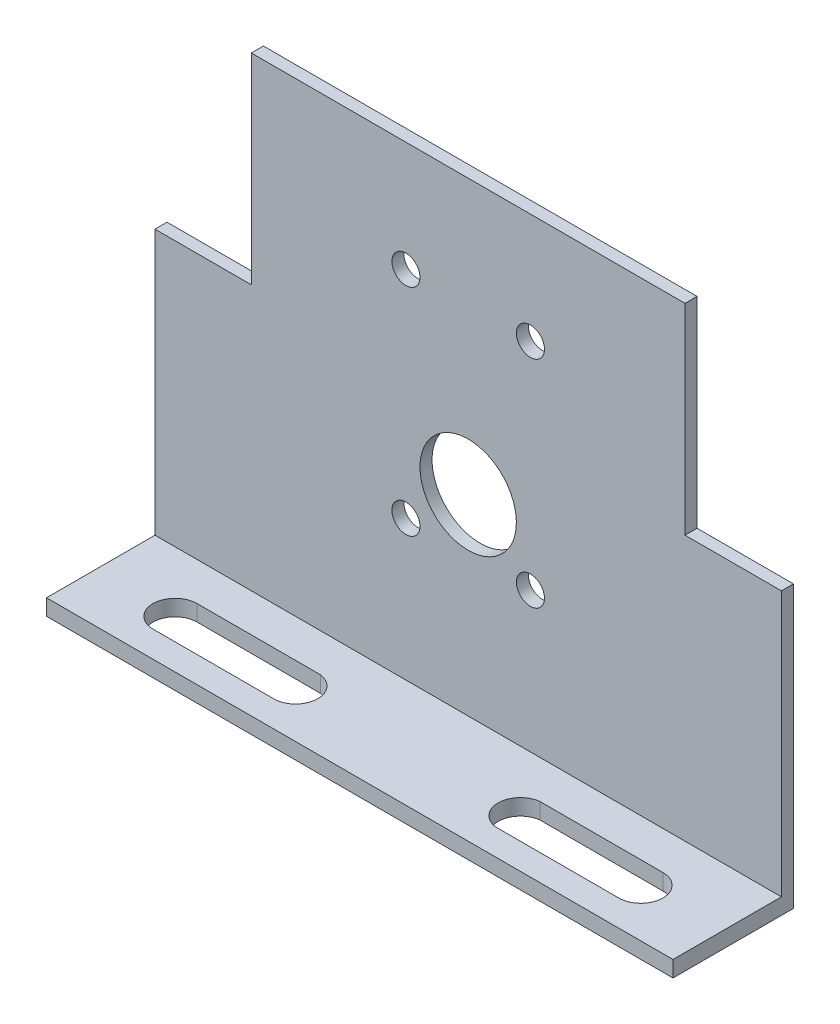
SolidWorks part; units mm, degrees
ref_plane "前视基准面" through (0, 0, 0) normal (0, 0, 1) x (1, 0, 0)
ref_plane "上视基准面" through (0, 0, 0) normal (0, 1, 0) x (1, 0, 0)
ref_plane "右视基准面" through (0, 0, 0) normal (1, 0, 0) x (0, 0, -1)
sketch "草图1" plane through (0, 0, 0) normal (0, 0, 1) x (1, 0, 0)
  line L0 (-78, 0) -> (0, 0)
  line L2 (0, 0) -> (0, 2)
  line L3 (-78, 0) -> (-78, 2)
  line L5 (-78, 2.7366) -> (-78, 2)
  line L6 (0, 2) -> (0, 2.7366)
  line L7 (-78, 2.7366) -> (-78, 35)
  line L8 (-78, 35) -> (-66, 35)
  line L9 (-66, 35) -> (-66, 60)
  line L10 (-66, 60) -> (-12, 60)
  line L11 (-12, 60) -> (-12, 35)
  line L12 (-12, 35) -> (0, 35)
  line L13 (0, 2.7366) -> (0, 35)
  line L22 (-48.675, 46.2927) -> (-44.825, 46.2927) construction
  line L23 (-46.75, 44.3677) -> (-46.75, 48.2177) construction
  line L24 (-33.175, 46.2927) -> (-29.325, 46.2927) construction
  line L25 (-31.25, 44.3677) -> (-31.25, 48.2177) construction
  line L26 (-48.675, 19.4459) -> (-44.825, 19.4459) construction
  line L27 (-46.75, 17.5209) -> (-46.75, 21.3709) construction
  line L28 (-33.175, 19.4459) -> (-29.325, 19.4459) construction
  line L29 (-31.25, 17.5209) -> (-31.25, 21.3709) construction
  line L30 (-45.6, 25.87) -> (-32.4, 25.87) construction
  line L31 (-39, 19.27) -> (-39, 32.47) construction
  circle A0 centre (-39, 25.87) radius 6
  circle A1 centre (-31.25, 19.4459) radius 1.75
  circle A2 centre (-46.75, 19.4459) radius 1.75
  circle A3 centre (-46.75, 46.2927) radius 1.75
  circle A4 centre (-31.25, 46.2927) radius 1.75
extrude "凸台-拉伸1" add sketch "草图1" along normal blind 1.5
sketch "草图2" plane through (0, 0, 0) normal (0, 0, -1) x (-1, 0, 0)
  line L0 (0, 0) -> (0, 35) construction
  line L1 (78, 0) -> (0, 0)
  line L2 (78, 0) -> (78, 2)
  line L3 (78, 2) -> (0, 2)
  line L4 (0, 0) -> (0, 2)
  dimension "D1" = 2
extrude "凸台-拉伸2" add sketch "草图2" against normal blind 15
sketch "草图3" plane through (0, 0, 0) normal (0, -1, 0) x (1, 0, 0)
  line L0 (-39, 15) -> (-39, 0) construction
  line L1 (-68, 11.75) -> (-52.6688, 11.75)
  line L2 (-10, 6.25) -> (-25.3312, 6.25)
  line L3 (-68, 6.25) -> (-52.6688, 6.25)
  line L4 (-10, 11.75) -> (-25.3312, 11.75)
  line L5 (0, 15) -> (-78, 15) construction
  line L6 (-78, 0) -> (0, 0) construction
  line L7 (-68, 9) -> (-53, 9) construction
  arc A0 (-68, 11.75) -> (-68, 6.25) centre (-68, 9) ccw
  arc A1 (-52.6688, 6.25) -> (-52.6688, 11.75) centre (-53, 9) ccw
  arc A2 (-25.3312, 6.25) -> (-25.3312, 11.75) centre (-25, 9) cw
  arc A3 (-10, 11.75) -> (-10, 6.25) centre (-10, 9) cw
  dimension "D1" = 5.5
  dimension "D2" = 6
  dimension "D3" = 28
  dimension "D4" = 58
extrude "切除-拉伸1" cut sketch "草图3" against normal blind 15
